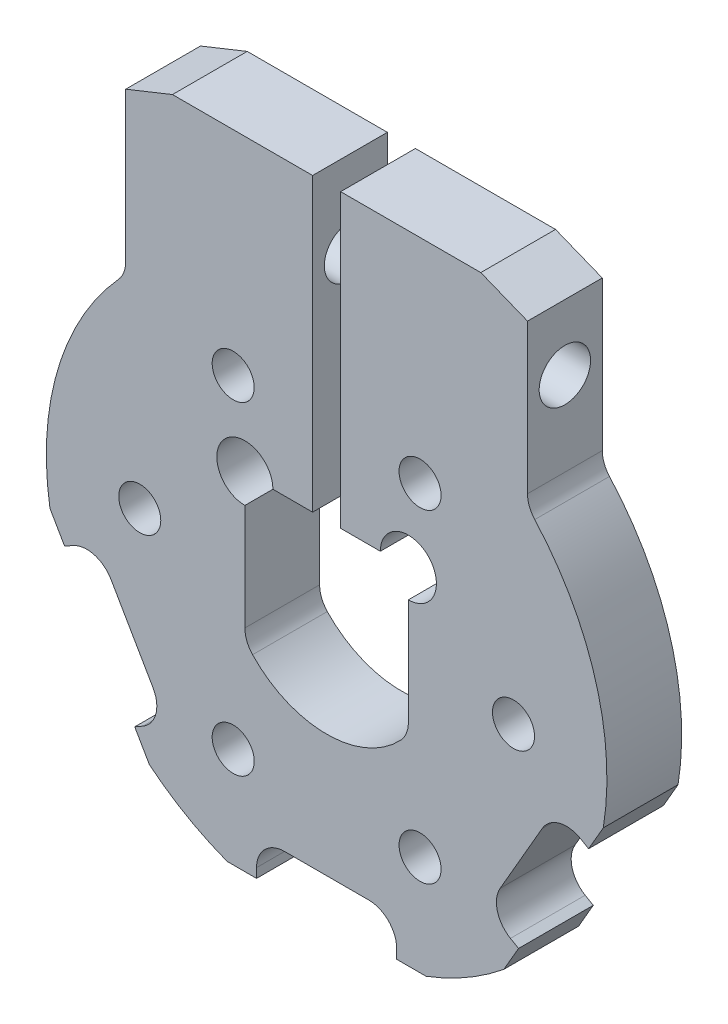
SolidWorks part; units mm, degrees
material "7075-T6 (SN)"
ref_plane "Ebene vorne" through (0, 0, 0) normal (0, 0, 1) x (1, 0, 0)
ref_plane "Ebene oben" through (0, 0, 0) normal (0, 1, 0) x (1, 0, 0)
ref_plane "Ebene rechts" through (0, 0, 0) normal (1, 0, 0) x (0, 0, -1)
sketch "Skizze1" plane through (0, 0, 0) normal (0, 0, 1) x (1, 0, 0)
  line L0 (4.5, -24.0474) -> (-4.5, -24.0474)
  line L1 (-7.5, -27.0474) -> (-7.5, -28.0474)
  line L2 (-7.5, -28.0474) -> (-10.6463, -28.0474)
  line L3 (-18.9666, -23.2437) -> (-20.5397, -20.5189)
  line L4 (-20.5397, -20.5189) -> (-19.6737, -20.0189)
  line L5 (-18.5756, -15.9208) -> (-23.0756, -8.1266)
  line L6 (-27.1737, -7.0285) -> (-28.0397, -7.5285)
  line L7 (-28.0397, -7.5285) -> (-29.6129, -4.8037)
  line L8 (-21.5, 22.1077) -> (-21.5, 38.1077)
  line L9 (-21.5, 38.1077) -> (-16.5, 40.1077)
  line L10 (-16.5, 40.1077) -> (-1.5, 40.1077)
  line L11 (-1.5, 40.1077) -> (-1.5, 8.9)
  line L12 (-1.5, 8.9) -> (-5.75, 8.9)
  line L13 (-8.75, 5.9) -> (-8.75, -5.4593)
  line L14 (8.75, -5.4593) -> (8.75, 5.9)
  line L15 (5.75, 8.9) -> (1.5, 8.9)
  line L16 (1.5, 8.9) -> (1.5, 40.1077)
  line L17 (1.5, 40.1077) -> (16.5, 40.1077)
  line L18 (16.5, 40.1077) -> (21.5, 38.1077)
  line L19 (21.5, 38.1077) -> (21.5, 22.1077)
  line L20 (29.6129, -4.8037) -> (28.0397, -7.5285)
  line L21 (28.0397, -7.5285) -> (27.1737, -7.0285)
  line L22 (23.0756, -8.1266) -> (18.5756, -15.9208)
  line L23 (19.6737, -20.0189) -> (20.5397, -20.5189)
  line L24 (20.5397, -20.5189) -> (18.9666, -23.2437)
  line L25 (10.6463, -28.0474) -> (7.5, -28.0474)
  line L26 (7.5, -28.0474) -> (7.5, -27.0474)
  line L27 (0, 48.7795) -> (0, -48.7795) construction
  line L28 (-5.75, 8.9) -> (-8.75, 8.9) construction
  line L29 (-8.75, 8.9) -> (-8.75, 5.9) construction
  line L30 (5.75, 8.9) -> (8.75, 8.9) construction
  line L31 (8.75, 8.9) -> (8.75, 5.9) construction
  line L32 (-20.8256, -12.0237) -> (0, 0) construction
  line L33 (0, 0) -> (20.8256, -12.0237) construction
  arc A6 (-4.5, -24.0474) -> (-7.5, -27.0474) centre (-4.5, -27.0474) ccw
  arc A7 (-18.9666, -23.2437) -> (-10.6463, -28.0474) centre (0, 0) ccw
  arc A8 (-19.6737, -20.0189) -> (-18.5756, -15.9208) centre (-21.1737, -17.4208) ccw
  arc A9 (-23.0756, -8.1266) -> (-27.1737, -7.0285) centre (-25.6737, -9.6266) ccw
  arc A10 (-22.2727, 20.0979) -> (-29.6129, -4.8037) centre (0, 0) ccw
  arc A11 (-22.2727, 20.0979) -> (-21.5, 22.1077) centre (-24.5, 22.1077) ccw
  arc A12 (-5.75, 8.9) -> (-8.75, 5.9) centre (-8.75, 8.9) ccw
  arc A13 (-8.75, -5.4593) -> (-7.9256, -7.525) centre (-5.75, -5.4593) ccw
  arc A14 (-7.9256, -7.525) -> (7.9256, -7.525) centre (0, 0) ccw
  arc A15 (7.9256, -7.525) -> (8.75, -5.4593) centre (5.75, -5.4593) ccw
  arc A16 (8.75, 5.9) -> (5.75, 8.9) centre (8.75, 8.9) ccw
  arc A17 (21.5, 22.1077) -> (22.2727, 20.0979) centre (24.5, 22.1077) ccw
  arc A18 (29.6129, -4.8037) -> (22.2727, 20.0979) centre (0, 0) ccw
  arc A19 (27.1737, -7.0285) -> (23.0756, -8.1266) centre (25.6737, -9.6266) ccw
  arc A20 (18.5756, -15.9208) -> (19.6737, -20.0189) centre (21.1737, -17.4208) ccw
  arc A21 (10.6463, -28.0474) -> (18.9666, -23.2437) centre (0, 0) ccw
  arc A22 (7.5, -27.0474) -> (4.5, -24.0474) centre (4.5, -27.0474) ccw
  circle A23 centre (0, 0) radius 30 construction
  point P0 (0, -24.0474)
  point P3 (0, 0)
  dimension "D10" = 10.9289
  dimension "D12" = 3
  dimension "D13" = 60
  dimension "D1" = 43
  dimension "D2" = 3
  dimension "D3" = 5
  dimension "D4" = 2
  dimension "D5" = 9
  dimension "D6" = 3.1463
  dimension "D7" = 4
  dimension "D9" = 17.5
  dimension "D11" = 8.9
  dimension "D14" = 60
  dimension "D16" = 18
  dimension "D17" = 4
  dimension "D18" = 4
extrude "Aufsatz-Linear austragen1" add sketch "Skizze1" along normal blind 8
hole_wizard "Durchgangsloch für M5" positions "Skizze2" profile "Skizze3" hole size "M5" standard "DIN" end condition through all
sketch "Skizze2" plane through (21.5, 0, 0) normal (1, 0, 0) x (0, 0, -1)
  line L0 (-4, 40.1077) -> (-4, 22.1077) construction
  line L1 (-8, 40.1077) -> (0, 40.1077) construction
  point P0 (-4, 31.1077)
  point P12 (-4, 31.1077)
  dimension "D1" = 18
sketch "Skizze3" plane through (21.5, 31.1077, 4) normal (0, 1, 0) x (0, 0, -1)
  line L0 (0, 0) -> (0, 51.5)
  line L1 (0, 51.5) -> (2.75, 51.5)
  line L2 (2.75, 51.5) -> (2.75, 0)
  line L5 (2.75, 0) -> (0, 0)
  line L11 (0, -6.35) -> (0, 107.95) construction
  dimension "Bohrerdurchmesser" = 5.5
  dimension "Bohrungstiefe" = 51.5
hole_wizard "Durchgangsloch für M4" positions "Skizze6" profile "Skizze7" hole size "M4" standard "DIN" end condition through all
sketch "Skizze6" plane through (0, 0, 8) normal (0, 0, 1) x (1, 0, 0)
  line L0 (0, -24.0474) -> (0, 34.4221) construction
  line L1 (-4.5, -24.0474) -> (4.5, -24.0474) construction
  line L3 (0, 0) -> (-10, 17.3205) construction
  arc A0 (-7.9256, -7.525) -> (7.9256, -7.525) centre (0, 0) ccw construction
  arc A1 (-7.9256, -7.525) -> (7.9256, -7.525) centre (0, 0) ccw
  circle A2 centre (0, 0) radius 20 construction
  point P15 (-10, 17.3205)
  point P46 (10, 17.3205)
  point P47 (20, 0)
  point P48 (10, -17.3205)
  point P49 (-10, -17.3205)
  point P50 (-20, 0)
  dimension "D1" = 40
  dimension "D2" = 30
  dimension "D3" = 6
sketch "Skizze7" plane through (-20, 0, 8) normal (1, 0, 0) x (0, -1, 0)
  line L0 (0, 0) -> (0, 8)
  line L1 (0, 8) -> (2.25, 8)
  line L2 (2.25, 8) -> (2.25, 0)
  line L5 (2.25, 0) -> (0, 0)
  line L11 (0, -6.35) -> (0, 107.95) construction
  dimension "Bohrerdurchmesser" = 4.5
  dimension "Bohrungstiefe" = 8
